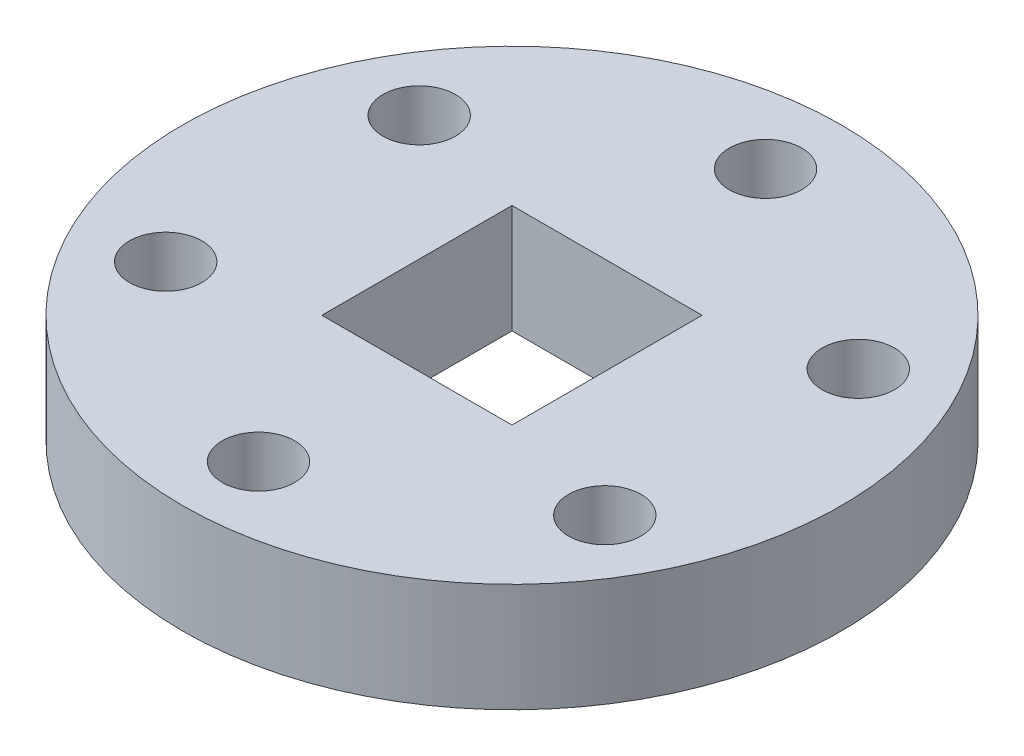
SolidWorks part; units mm, degrees
ref_plane "Front Plane" through (0, 0, 0) normal (0, 0, 1) x (1, 0, 0)
ref_plane "Top Plane" through (0, 0, 0) normal (0, 1, 0) x (1, 0, 0)
ref_plane "Right Plane" through (0, 0, 0) normal (1, 0, 0) x (0, 0, -1)
sketch "Sketch1" plane through (0, 0, 0) normal (0, 1, 0) x (1, 0, 0)
  circle A0 centre (0, 0) radius 18.2
  dimension "D1" = 36.4
extrude "Boss-Extrude1" add sketch "Sketch1" along normal blind 6 contours A0
sketch "Sketch2" plane through (0, 6, 0) normal (0, 1, 0) x (1, 0, 0)
  circle A0 centre (0, 14) radius 2
  circle A1 centre (12.1244, 7) radius 2
  circle A2 centre (12.1244, -7) radius 2
  circle A3 centre (0, -14) radius 2
  circle A4 centre (-12.1244, -7) radius 2
  circle A5 centre (-12.1244, 7) radius 2
  dimension "D1" = 14
  dimension "D2" = 6
extrude "Cut-Extrude1" cut sketch "Sketch2" against normal blind 6
sketch "Sketch3" plane through (0, 6, 0) normal (0, 1, 0) x (1, 0, 0)
  line L1 (-5.25, 5.25) -> (5.25, 5.25)
  line L2 (-5.25, 5.25) -> (-5.25, -5.25)
  line L3 (-5.25, -5.25) -> (5.25, -5.25)
  line L4 (5.25, 5.25) -> (5.25, -5.25)
  line L5 (-5.25, 5.25) -> (5.25, -5.25) construction
  line L6 (-5.25, -5.25) -> (5.25, 5.25) construction
  point P0 (0, 0)
extrude "Cut-Extrude2" cut sketch "Sketch3" against normal blind 6 contours L1 L4 L3 L2
